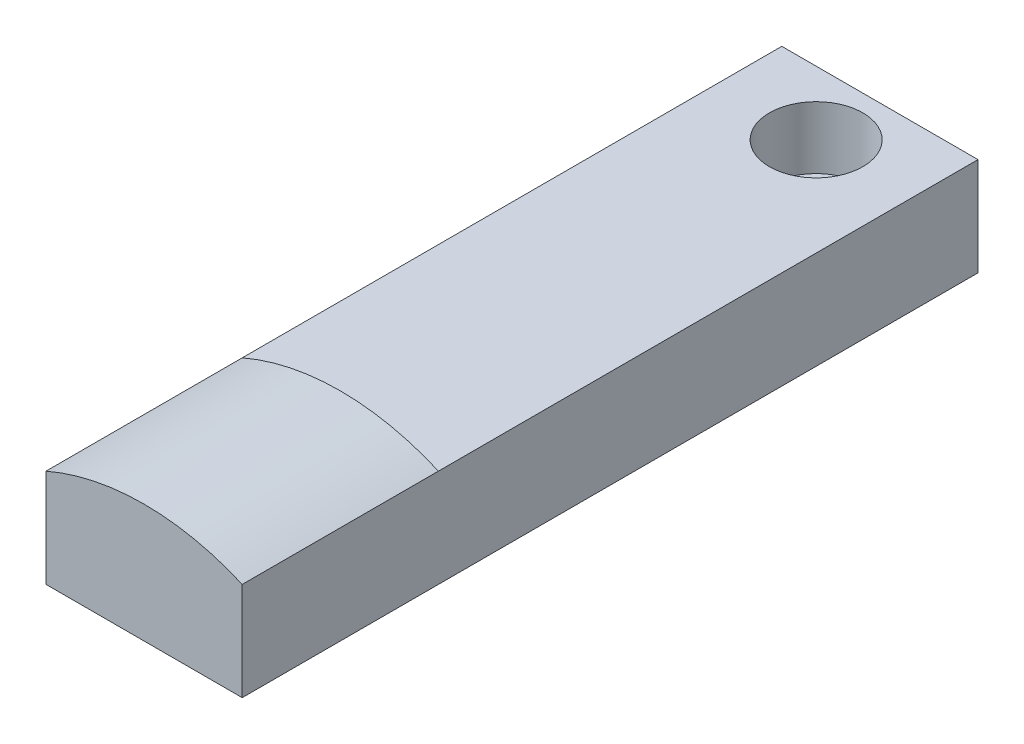
SolidWorks part; units mm, degrees
ref_plane "Plano frontal" through (0, 0, 0) normal (0, 0, 1) x (1, 0, 0)
ref_plane "Plano superior" through (0, 0, 0) normal (0, 1, 0) x (1, 0, 0)
ref_plane "Plano direito" through (0, 0, 0) normal (1, 0, 0) x (0, 0, -1)
sketch "Esboço1" plane through (0, 0, 0) normal (0, 0, 1) x (1, 0, 0)
  line L1 (10, -5) -> (-10, -5)
  line L2 (10, -5) -> (10, 5)
  line L3 (10, 5) -> (-10, 5)
  line L4 (-10, -5) -> (-10, 5)
  line L5 (10, -5) -> (-10, 5) construction
  line L6 (10, 5) -> (-10, -5) construction
  point P0 (0, 0)
  dimension "D1" = 20
  dimension "D2" = 10
extrude "Ressalto-extrusão1" add sketch "Esboço1" along normal blind 75
hole_wizard "Furo1" positions "Esboço2" profile "Esboço3" legacy
sketch "Esboço2" plane through (0, 5, 0) normal (0, 1, 0) x (1, 0, 0)
  line L0 (-10, -75) -> (-10, 0) construction
  line L1 (10, 0) -> (-10, 0) construction
  point P0 (0, -6.5)
  dimension "D1" = 10
  dimension "D2" = 6.5
sketch "Esboço3" plane through (0, 5, 6.5) normal (1, 0, 0) x (0, 0, 1)
  line L0 (0, 0) -> (0, 14.916)
  line L1 (0, 14.916) -> (3.175, 14.916)
  line L2 (3.175, 14.916) -> (3.175, 6.35)
  line L3 (3.175, 6.35) -> (4.76, 6.35)
  line L4 (4.76, 6.35) -> (4.76, 0)
  line L5 (4.76, 0) -> (0, 0)
  line L6 (0, 110) -> (0, -10) construction
  dimension "Diameter" = 6.35
  dimension "Depth" = 15
  dimension "C-Bore Diameter" = 9.52
  dimension "C-Bore Depth" = 6.35
sketch "Esboço4" plane through (0, 0, 75) normal (0, 0, 1) x (1, 0, 0)
  line L0 (0, 6.6958) -> (0, -8.4132) construction
  line L1 (-10, 5) -> (10, 5)
  line L2 (10, 5) -> (-10, 5) construction
  line L3 (-10, 5) -> (-10, -5) construction
  arc A1 (10, 5) -> (-10, 5) centre (0, -17.9129) ccw
  point P8 (0, 0)
  point P13 (0, 0)
  dimension "D1" = 50
extrude "Ressalto-extrusão2" add sketch "Esboço4" against normal blind 20
